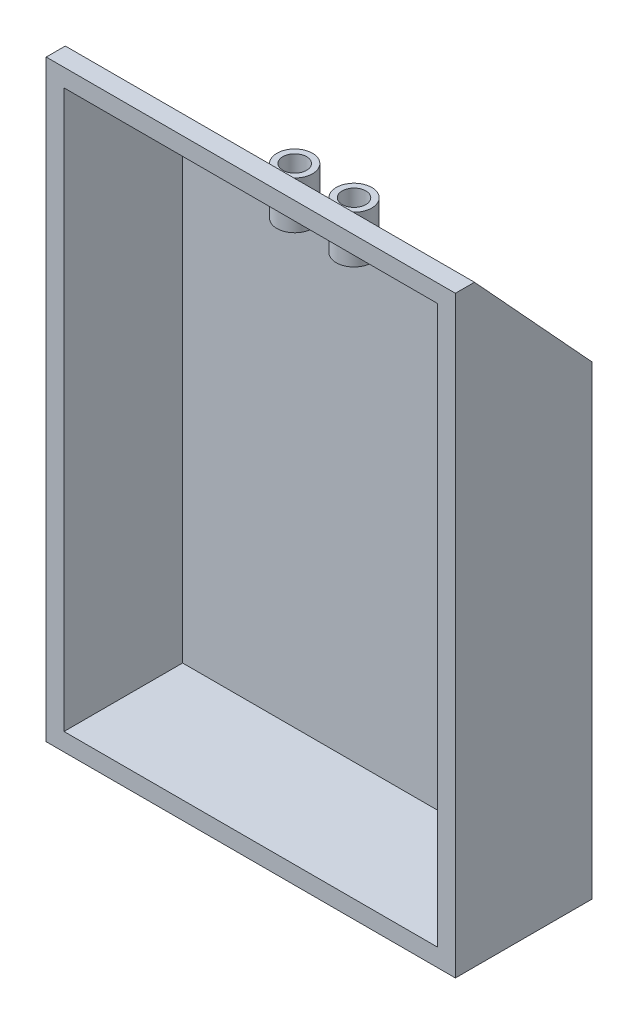
SolidWorks part; units mm, degrees
ref_plane "Ön Düzlem" through (0, 0, 0) normal (0, 0, 1) x (1, 0, 0)
ref_plane "Üst Düzlem" through (0, 0, 0) normal (0, 1, 0) x (1, 0, 0)
ref_plane "Sağ Düzlem" through (0, 0, 0) normal (1, 0, 0) x (0, 0, -1)
sketch "Çizim1" plane through (0, 0, 0) normal (0, 0, 1) x (1, 0, 0)
  line L0 (-34.5, 50) -> (34.5, -50) construction
  line L1 (-34.5, 50) -> (34.5, 50)
  line L2 (-34.5, 50) -> (-34.5, -50)
  line L3 (-34.5, -50) -> (34.5, -50)
  line L4 (34.5, 50) -> (34.5, -50)
  dimension "D1" = 100
  dimension "D2" = 69
extrude "Yükseklik-Ekstrüzyon1" add sketch "Çizim1" along normal blind 3
sketch "Çizim2" plane through (0, 0, 3) normal (0, 0, 1) x (1, 0, 0)
  line L0 (-31.5, 47) -> (-31.5, -47)
  line L1 (-34.5, 50) -> (34.5, 50)
  line L2 (-34.5, 50) -> (-34.5, -50)
  line L3 (-34.5, -50) -> (34.5, -50)
  line L4 (34.5, 50) -> (34.5, -50)
  line L5 (-31.5, -47) -> (31.5, -47)
  line L6 (31.5, 47) -> (31.5, -47)
  line L7 (-31.5, 47) -> (31.5, 47)
  dimension "D1" = 3
extrude "Yükseklik-Ekstrüzyon2" add sketch "Çizim2" along normal blind 20
sketch "Çizim3" plane through (34.5, 0, 0) normal (1, 0, 0) x (0, 0, -1)
  line L0 (-23, 50) -> (0, 25)
  line L1 (0, -50) -> (0, 50) construction
  line L2 (0, 25) -> (0, 50)
  line L3 (0, 50) -> (-23, 50)
extrude "Kes-Ekstrüzyon1" cut sketch "Çizim3" against normal through all
sketch "Çizim4" plane through (34.5, 0, 0) normal (1, 0, 0) x (0, 0, -1)
  line L0 (-23, 50) -> (-19.78, 50)
  line L1 (-19.78, 50) -> (0, 28.5)
  line L2 (0, 28.5) -> (0, 25)
  line L3 (0, 25) -> (-23, 50)
  dimension "D1" = 3.5
extrude "Yükseklik-Ekstrüzyon3" add sketch "Çizim4" against normal through all
sketch "Çizim5" plane through (0, 50, 0) normal (0, 1, 0) x (1, 0, 0)
  line L1 (-34.5, 0) -> (-34.5, -19.78) construction
  circle A0 centre (-5, -10.5942) radius 3
  circle A1 centre (5, -10.5942) radius 3
  dimension "D1" = 10
  dimension "D2" = 29.5
extrude "Kes-Ekstrüzyon2" cut sketch "Çizim5" against normal blind 20
sketch "Çizim6" plane through (0, 50, 0) normal (0, 1, 0) x (1, 0, 0)
  circle A0 centre (-5, -10.5942) radius 3
  circle A1 centre (-5, -10.5942) radius 2
  circle A2 centre (5, -10.5942) radius 3
  circle A3 centre (5, -10.5942) radius 2
extrude "Yükseklik-Ekstrüzyon4" add sketch "Çizim6" along normal blind 8 from offset 15
